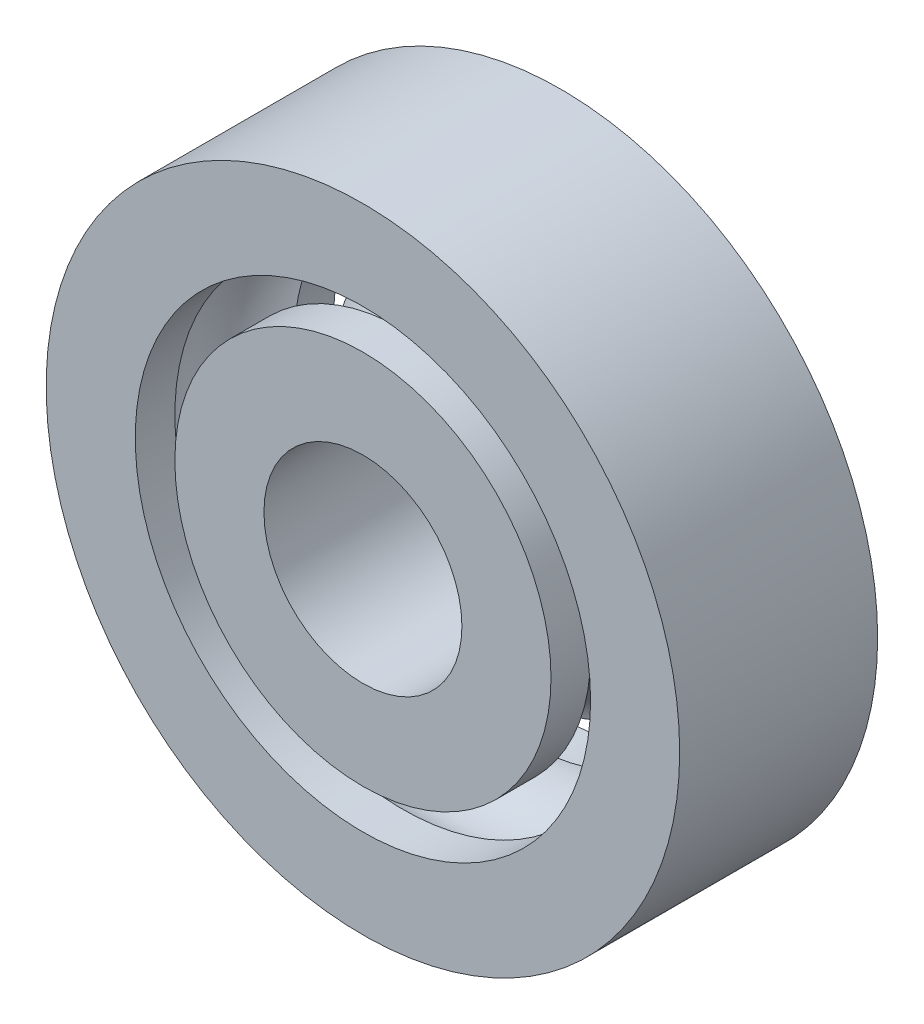
SolidWorks part; units mm, degrees
ref_plane "Front Plane" through (0, 0, 0) normal (0, 0, 1) x (1, 0, 0)
ref_plane "Top Plane" through (0, 0, 0) normal (0, 1, 0) x (1, 0, 0)
ref_plane "Right Plane" through (0, 0, 0) normal (1, 0, 0) x (0, 0, -1)
sketch "Sketch3" plane through (0, 0, 0) normal (1, 0, 0) x (0, 0, -1)
  line L0 (55, 0) -> (-55, 0) construction
  line L2 (-2.5, 2.5) -> (-2.5, 4.75)
  line L3 (-2.5, 8) -> (2.5, 8)
  line L4 (2.5, 2.5) -> (2.5, 4.75)
  line L5 (-2.5, 2.5) -> (2.5, 2.5)
  line L6 (0, 8) -> (0, 0) construction
  line L7 (0, 55) -> (0, -55) construction
  line L8 (-2.5, 0) -> (2.5, 0) construction
  line L9 (-2.5, 5.75) -> (-1.5, 5.75)
  line L10 (2.5, 5.75) -> (1.5, 5.75)
  line L11 (-2.5, 4.75) -> (-1.5, 4.75)
  line L12 (2.5, 4.75) -> (1.5, 4.75)
  line L13 (2.5, 5.75) -> (2.5, 8)
  line L14 (-2.5, 5.75) -> (-2.5, 8)
  arc A0 (-1.5, 5.75) -> (1.5, 5.75) centre (0, 5.25) cw
  arc A1 (-1.5, 4.75) -> (1.5, 4.75) centre (0, 5.25) ccw
  dimension "D7" = 1.5811
  dimension "D1" = 2.5
  dimension "D2" = 8
  dimension "D3" = 5
  dimension "D4" = 1
  dimension "D5" = 2.25
  dimension "D6" = 2.25
revolve "Revolve1" add sketch "Sketch3" angle 360 about L8
